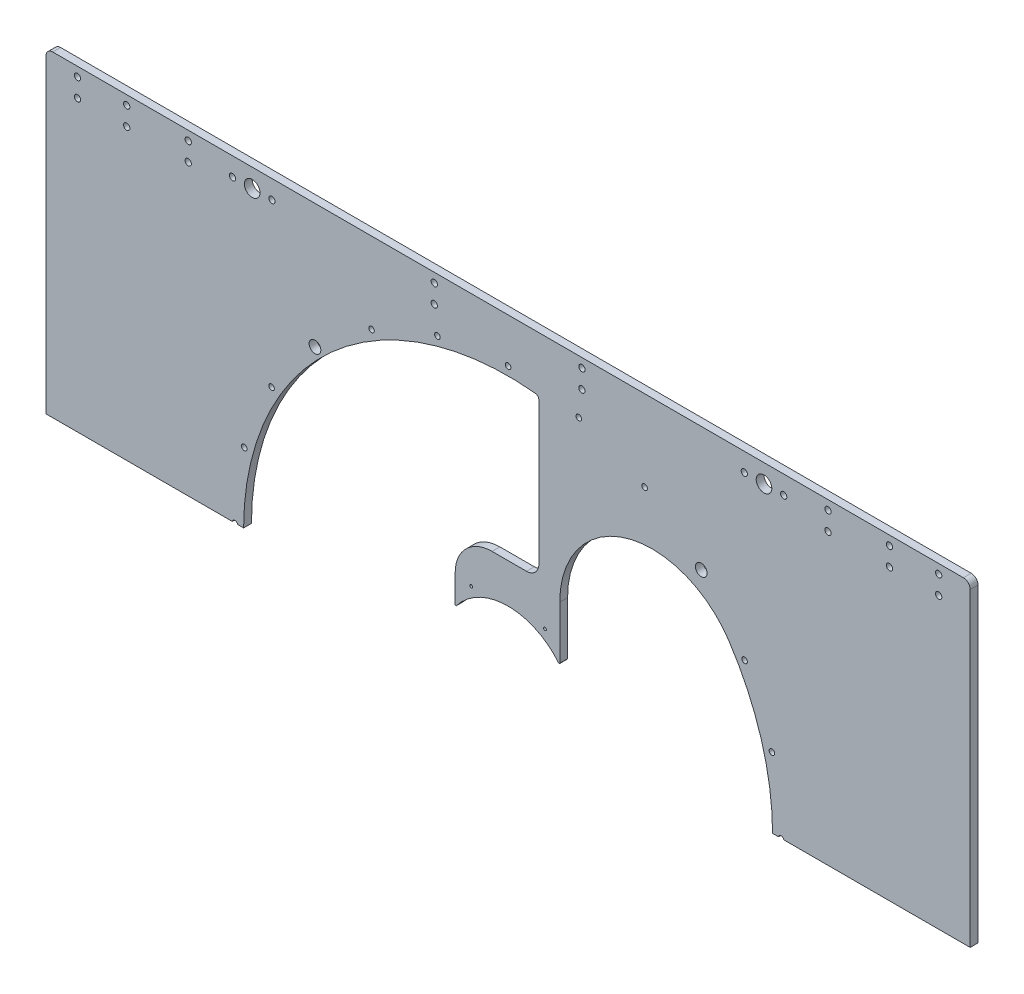
SolidWorks part; units mm, degrees
material "6061-T6 (SS)"
ref_plane "Front Plane" through (0, 0, 0) normal (0, 0, 1) x (1, 0, 0)
ref_plane "Top Plane" through (0, 0, 0) normal (0, 1, 0) x (1, 0, 0)
ref_plane "Right Plane" through (0, 0, 0) normal (1, 0, 0) x (0, 0, -1)
sketch "Sketch1" plane through (0, 0, 0) normal (0, 0, 1) x (1, 0, 0)
  line L0 (375.6002, 258) -> (-375.6002, -258) construction
  line L1 (375.6002, 258) -> (-375.6002, 258)
  line L2 (375.6002, 258) -> (375.6002, -258)
  line L3 (375.6002, -258) -> (-375.6002, -258)
  line L4 (-375.6002, 258) -> (-375.6002, -258)
  line L5 (25, 213.5164) -> (25, 85)
  line L6 (0, 0) -> (0, -60.487) construction
  line L7 (0, 0) -> (-63.8539, 0) construction
  line L8 (-25, -63) -> (-25, -213.5164)
  line L9 (25, 129.4291) -> (-25, 129.4291) construction
  line L10 (42, 210.8323) -> (42, 27.3132)
  line L11 (-42, -210.8323) -> (-42, -27.3132)
  line L12 (-25, -63) -> (17.7051, -46.8673)
  line L14 (-43, 25.7101) -> (-43, 85)
  line L15 (-43, 85) -> (25, 85)
  circle A0 centre (0, 0) radius 42.5 construction
  circle A1 centre (0, 0) radius 214.975 construction
  circle A2 centre (0, 0) radius 222 construction
  circle A3 centre (0, 0) radius 227.325 construction
  circle A4 centre (0, 0) radius 42.5
  arc A5 (-43, 25.7101) -> (-42, -27.3132) centre (0, 0) ccw
  arc A6 (25, 213.5164) -> (-42, -210.8323) centre (0, 0) ccw
  arc A7 (17.7051, -46.8673) -> (42, 27.3132) centre (0, 0) ccw
  arc A8 (-25, -213.5164) -> (42, 210.8323) centre (0, 0) ccw
  point P10 (0, 0)
  point P21 (0, 129.4291)
  dimension "D1" = 85
  dimension "D2" = 429.95
  dimension "D3" = 444
  dimension "D4" = 454.65
  dimension "D7" = 100.2
  dimension "D5" = 516
  dimension "D6" = 25
  dimension "D8" = 17
  dimension "D9" = 17
  dimension "D10" = 63
  dimension "D11" = 85
  dimension "D12" = 68
  dimension "D13" = 751.2004
extrude "Boss-Extrude2" add sketch "Sketch1" along normal mid plane 6.35
fillet "Fillet1" radius 25 3 edges at (-42, -27.3132, 0) (-25, -63, 0) (42, 27.3132, 0)
fillet "Fillet4" radius 75 2 edges at (-42, -210.8323, 0) (42, 210.8323, 0)
sketch "Sketch2" plane through (0, 0, -3.175) normal (0, 0, -1) x (-1, 0, 0)
  line L0 (-375.6002, -258) -> (-375.6002, 258) construction
  line L1 (-375.6002, 0) -> (375.6002, 0)
  line L2 (-375.6002, 0) -> (-375.6002, -258)
  line L3 (-375.6002, -258) -> (375.6002, -258)
  line L4 (375.6002, 0) -> (375.6002, -258)
extrude "Cut-Extrude1" cut sketch "Sketch2" against normal blind 10
fillet "Fillet6" radius 10 2 edges at (-43, 25.7101, 0) (25, 85, 0)
fillet "Fillet7" radius 30 1 edges at (-43, 85, 0)
sketch "Sketch3" plane through (0, 0, -3.175) normal (0, 0, -1) x (-1, 0, 0)
  line L0 (0, 0) -> (0, 311.2393) construction
  line L1 (0, 235.5) -> (-45.4507, 235.5) construction
  line L2 (0, 250.5) -> (-41.1707, 250.5) construction
  line L3 (0, 0) -> (-18.1608, 0) construction
  line L4 (60, -67.2639) -> (60, 99.0215) construction
  line L5 (350, -84.5281) -> (350, 60.5139) construction
  line L6 (-375.6002, 258) -> (375.6002, 258) construction
  line L7 (285, -84.5281) -> (285, 352.8717) construction
  line L8 (310, 235.5) -> (310, 250.5) construction
  line L9 (-310, 235.5) -> (-310, 250.5) construction
  line L10 (208, -123.9272) -> (208, 43.0912) construction
  line L11 (224, 243) -> (192, 243) construction
  line L12 (-224, 243) -> (-192, 243) construction
  point P14 (350, 250.5)
  point P15 (350, 235.5)
  point P16 (60, 250.5)
  point P17 (60, 235.5)
  point P18 (-60, 250.5)
  point P19 (-350, 250.5)
  point P20 (-60, 235.5)
  point P21 (-350, 235.5)
  point P24 (310, 235.5)
  point P25 (310, 250.5)
  point P28 (260, 250.5)
  point P29 (260, 235.5)
  point P30 (-260, 250.5)
  point P31 (-260, 235.5)
  point P41 (-208, 243)
  point P43 (208, 243)
  dimension "D1" = 7.5
  dimension "D2" = 22.5
  dimension "D3" = 350
  dimension "D4" = 60
  dimension "D5" = 285
  dimension "D6" = 25
  dimension "D7" = 208
  dimension "D8" = 32
  dimension "D9" = 15
hole_wizard "CSK for #10 Flat Head Machine Screw1" positions "Sketch5" profile "Sketch4" countersink size "#10" standard "ANSI Inch" end condition through all
sketch "Sketch5" plane through (0, 0, -3.175) normal (0, 0, -1) x (-1, 0, 0)
  point P0 (350, 235.5)
  point P3 (350, 250.5)
  point P5 (60, 235.5)
  point P8 (60, 250.5)
  point P11 (-60, 235.5)
  point P14 (-60, 250.5)
  point P17 (-350, 235.5)
  point P20 (-350, 250.5)
  point P27 (310, 235.5)
  point P30 (310, 250.5)
  point P33 (260, 235.5)
  point P36 (260, 250.5)
  point P39 (-310, 235.5)
  point P42 (-310, 250.5)
  point P45 (-260, 235.5)
  point P48 (-260, 250.5)
  point P51 (224, 243)
  point P54 (192, 243)
  point P58 (-224, 243)
  point P61 (-192, 243)
sketch "Sketch4" plane through (-350, 235.5, -3.175) normal (1, 0, 0) x (0, 1, 0)
  line L0 (0, 0) -> (0, 6.35)
  line L1 (0, 6.35) -> (2.5527, 6.35)
  line L2 (2.5527, 6.35) -> (2.5527, 2.6882)
  line L3 (2.5527, 2.6882) -> (4.8895, 0)
  line L5 (4.8895, 0) -> (0, 0)
  line L6 (-2.5527, 2.6882) -> (-4.8895, 0) construction
  line L11 (0, -6.35) -> (0, 107.95) construction
  dimension "Thru Hole Dia." = 5.1054
  dimension "Thru Hole Depth" = 6.35
  dimension "Near C'Sink Dia." = 9.779
  dimension "Near C'Sink Angle" = 82
hole_wizard "1/2 (0.5) Diameter Hole1" positions "Sketch9" profile "Sketch8" hole size "1/2" standard "ANSI Inch"
sketch "Sketch9" plane through (0, 0, -3.175) normal (0, 0, -1) x (-1, 0, 0)
  point P0 (208, 243)
  point P3 (-208, 243)
sketch "Sketch8" plane through (-208, 243, -3.175) normal (1, 0, 0) x (0, 1, 0)
  line L0 (0, 0) -> (0, 133.3455)
  line L1 (0, 133.3455) -> (6.35, 129.53)
  line L2 (6.35, 129.53) -> (6.35, 0)
  line L5 (6.35, 0) -> (0, 0)
  line L10 (0, 133.3455) -> (-6.35, 129.53) construction
  line L11 (0, -6.35) -> (0, 107.95) construction
  dimension "Hole Dia." = 12.7
  dimension "Hole Depth" = 129.53
  dimension "Drill Angle" = 118
hole_wizard "CSK for M4 Flat Head Machine Screw1" positions "Sketch11" profile "Sketch10" countersink size "M4" standard "ANSI Metric" end condition through all
sketch "Sketch11" plane through (0, 0, -3.175) normal (0, 0, -1) x (-1, 0, 0)
  line L0 (0, 0) -> (0, 69.5623) construction
  line L2 (0, 0) -> (101.1814, 0) construction
  point P0 (0, 222)
  dimension "D1" = 222
sketch "Sketch10" plane through (0, 222, -3.175) normal (1, 0, 0) x (0, 1, 0)
  line L0 (0, 0) -> (0, 6.35)
  line L1 (0, 6.35) -> (2.25, 6.35)
  line L2 (2.25, 6.35) -> (2.25, 2.45)
  line L3 (2.25, 2.45) -> (4.7, 0)
  line L5 (4.7, 0) -> (0, 0)
  line L6 (-2.25, 2.45) -> (-4.7, 0) construction
  line L11 (0, -6.35) -> (0, 107.95) construction
  dimension "Thru Hole Dia." = 4.5
  dimension "Thru Hole Depth" = 6.35
  dimension "Near C'Sink Dia." = 9.4
  dimension "Near C'Sink Angle" = 90
pattern_circular "CirPattern1" count 24 over 360 about axis through (0, 0, 0) along (0, 0, 1) skipping 6, 7, 8, 9, 10, 11, 12, 13, 14, 15, 16, 17, 18 of "CSK for M4 Flat Head Machine Screw1"
hole_wizard "M4 Clearance Hole1" positions "Sketch15" profile "Sketch14" hole size "M4" standard "ANSI Metric" end condition through all
sketch "Sketch15" plane through (0, 0, -3.175) normal (0, 0, -1) x (-1, 0, 0)
  line L0 (0, 0) -> (-87.1517, 0) construction
  line L1 (0, 0) -> (0, -162.7163) construction
  point P0 (-222, 0)
  point P10 (222, 0)
  dimension "D1" = 222
sketch "Sketch14" plane through (222, 0, -3.175) normal (1, 0, 0) x (0, 1, 0)
  line L0 (0, 0) -> (0, 6.35)
  line L1 (0, 6.35) -> (2.25, 6.35)
  line L2 (2.25, 6.35) -> (2.25, 0)
  line L5 (2.25, 0) -> (0, 0)
  line L11 (0, -6.35) -> (0, 107.95) construction
  dimension "Thru Hole Dia." = 4.5
  dimension "Thru Hole Depth" = 6.35
sketch "Sketch12" plane through (0, 0, -3.175) normal (0, 0, -1) x (-1, 0, 0)
  line L0 (375.6002, 258) -> (375.6002, 0) construction
  line L1 (-375.6002, 0.5) -> (375.6002, 0.5)
  line L2 (-375.6002, 0.5) -> (-375.6002, -0.5)
  line L3 (-375.6002, -0.5) -> (375.6002, -0.5)
  line L4 (375.6002, 0.5) -> (375.6002, -0.5)
  line L5 (-375.6002, 0.5) -> (375.6002, -0.5) construction
  line L6 (-375.6002, -0.5) -> (375.6002, 0.5) construction
  point P0 (0, 0)
  dimension "D1" = 1
extrude "Cut-Extrude2" cut sketch "Sketch12" against normal through all
fillet "Fillet8" radius 3.175 1 edges at (25, 213.5164, 0)
fillet "Fillet9" radius 5.5 2 edges at (375.6002, 258, 0) (-375.6002, 258, 0)
hole_wizard "3/8 (0.375) Diameter Hole1 to clear  4 mm cap screw" positions "Sketch17" profile "Sketch16" hole size "3/8" standard "ANSI Inch" end condition through all
sketch "Sketch17" plane through (0, 0, -3.175) normal (0, 0, -1) x (-1, 0, 0)
  point P0 (-156.9777, 156.9777)
  point P3 (156.9777, 156.9777)
sketch "Sketch16" plane through (156.9777, 156.9777, -3.175) normal (1, 0, 0) x (0, 1, 0)
  line L0 (0, 0) -> (0, 6.35)
  line L1 (0, 6.35) -> (4.7625, 6.35)
  line L2 (4.7625, 6.35) -> (4.7625, 0)
  line L5 (4.7625, 0) -> (0, 0)
  line L11 (0, -6.35) -> (0, 107.95) construction
  dimension "Thru Hole Dia." = 9.525
  dimension "Thru Hole Depth" = 6.35
sketch "Sketch18" plane through (0, 0, -3.175) normal (0, 0, -1) x (-1, 0, 0)
  circle A0 centre (0, 0) radius 53
  dimension "D1" = 106
extrude "Cut-Extrude3" cut sketch "Sketch18" against normal through all
hole_wizard "#4-40 Tapped Hole1" positions "Sketch20" profile "Sketch19" tap size "#4-40" standard "ANSI Inch"
sketch "Sketch20" plane through (0, 0, -3.175) normal (0, 0, -1) x (-1, 0, 0)
  line L0 (0, 0) -> (0, 44.0924) construction
  point P0 (-30, 51.9615)
  point P8 (30, 51.9615)
  dimension "D1" = 60
  dimension "D2" = 60
sketch "Sketch19" plane through (30, 51.9615, -3.175) normal (1, 0, 0) x (0, 1, 0)
  line L0 (0, 0) -> (0, 10.2092)
  line L1 (0, 10.2092) -> (1.1303, 9.53)
  line L2 (1.1303, 9.53) -> (1.1303, 0)
  line L5 (1.1303, 0) -> (0, 0)
  line L10 (0, 10.2092) -> (-1.1303, 9.53) construction
  line L11 (0, -6.35) -> (0, 107.95) construction
  dimension "Tap Drill Dia." = 2.2606
  dimension "Tap Drill Depth" = 9.53
  dimension "Drill Angle" = 118
cosmetic thread "Hole Thread1" parameters "D1"=5.69, "D2"=2.8448
cosmetic thread "Hole Thread2" parameters "D1"=5.69, "D2"=2.8448
fillet "Fillet10" radius 0.5 2 edges at (-43, 30.9839, 0) (42.056, 32.2535, 0)
